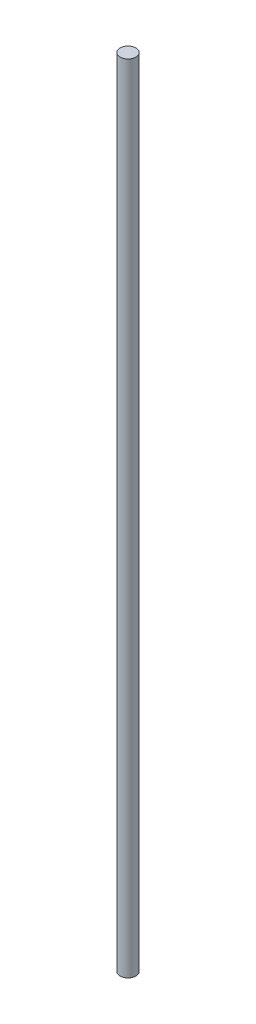
SolidWorks part; units mm, degrees
ref_plane "Front Plane" through (0, 0, 0) normal (0, 0, 1) x (1, 0, 0)
ref_plane "Top Plane" through (0, 0, 0) normal (0, 1, 0) x (1, 0, 0)
ref_plane "Right Plane" through (0, 0, 0) normal (1, 0, 0) x (0, 0, -1)
sketch "Sketch1" plane through (0, 0, 0) normal (0, 1, 0) x (1, 0, 0)
  circle A0 centre (0, 0) radius 4
  dimension "D1" = 8
extrude "Boss-Extrude1" add sketch "Sketch1" along normal blind 400
